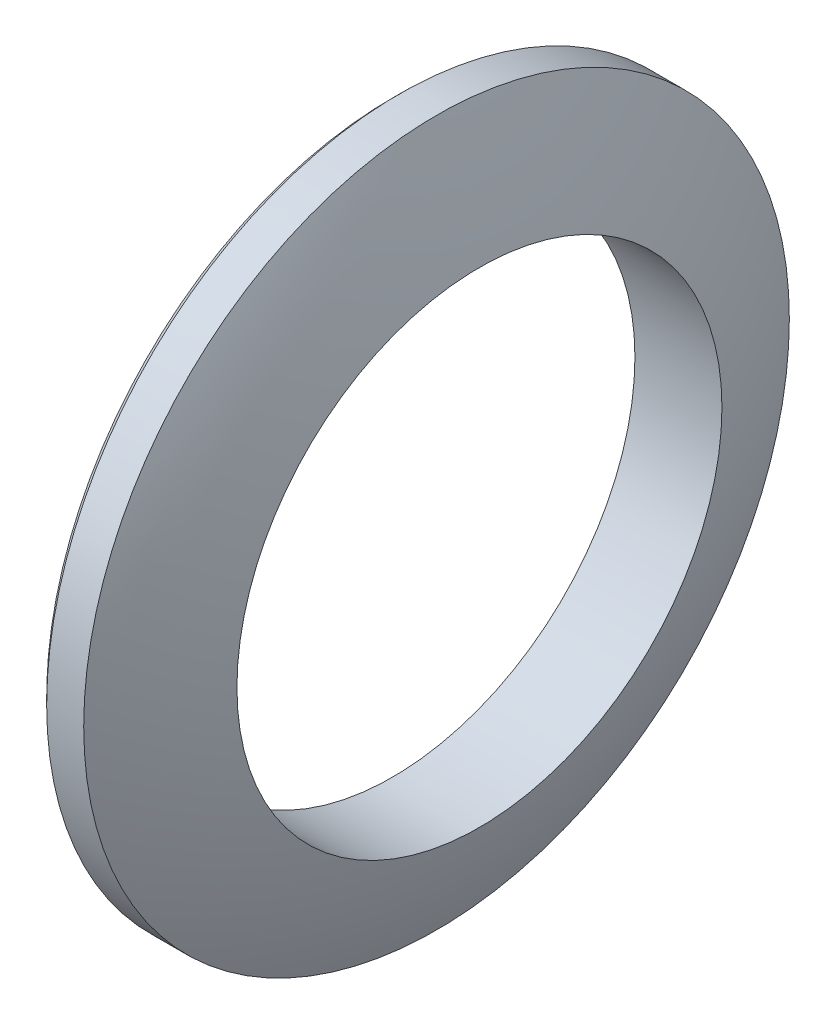
SolidWorks part; units mm, degrees
material "Alloy Steel"
ref_plane "Front" through (0, 0, 0) normal (0, 0, 1) x (1, 0, 0)
ref_plane "Top" through (0, 0, 0) normal (0, 1, 0) x (1, 0, 0)
ref_plane "Right" through (0, 0, 0) normal (1, 0, 0) x (0, 0, -1)
sketch "Sketch1" plane through (0, 0, 0) normal (0, 0, 1) x (1, 0, 0)
  line L0 (0, 0) -> (0, 26.1874) construction
  line L1 (0, 38.1) -> (4.7625, 38.1)
  line L2 (0, 38.1) -> (0, 26.1874)
  line L3 (0, 26.1874) -> (9.3961, 26.1874)
  line L4 (-75.5594, 0) -> (0, 0) construction
  line L5 (0, 0) -> (13.8441, 0) construction
  arc A0 (9.3961, 26.1874) -> (4.7625, 38.1) centre (-75.5594, 0) ccw
  dimension "D4" = 177.8
  dimension "D1" = 4.7625
  dimension "D2" = 76.2
  dimension "D3" = 52.3748
revolve "Revolve1" add sketch "Sketch1" angle 360 about L5
chamfer "Chamfer1" distance 0.762 angle 45 1 edges at (0, 0, 38.1)
